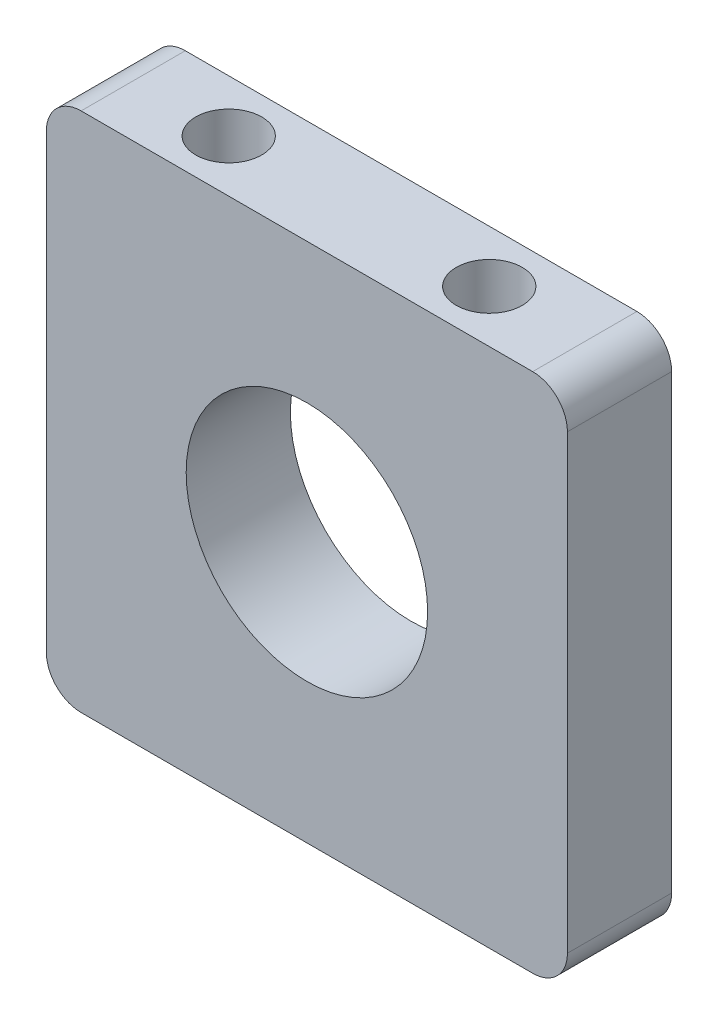
SolidWorks part; units mm, degrees
ref_plane "Front Plane" through (0, 0, 0) normal (0, 0, 1) x (1, 0, 0)
ref_plane "Top Plane" through (0, 0, 0) normal (0, 1, 0) x (1, 0, 0)
ref_plane "Right Plane" through (0, 0, 0) normal (1, 0, 0) x (0, 0, -1)
sketch "Sketch1" plane through (0, 0, 0) normal (0, 0, 1) x (1, 0, 0)
  line L1 (19.05, -19.05) -> (-19.05, -19.05)
  line L2 (19.05, -19.05) -> (19.05, 19.05)
  line L3 (19.05, 19.05) -> (-19.05, 19.05)
  line L4 (-19.05, -19.05) -> (-19.05, 19.05)
  line L5 (19.05, -19.05) -> (-19.05, 19.05) construction
  line L6 (19.05, 19.05) -> (-19.05, -19.05) construction
  circle A0 centre (0, 0) radius 8.8265
  point P0 (0, 0)
  dimension "D2" = 17.653
  dimension "D1" = 38.1
extrude "Boss-Extrude1" add sketch "Sketch1" along normal blind 7.62
fillet "Fillet1" radius 2.54 4 edges at (19.05, -19.05, 3.81) (-19.05, -19.05, 3.81) (-19.05, 19.05, 3.81) (19.05, 19.05, 3.81)
sketch "Sketch2" plane through (0, -19.05, 0) normal (0, -1, 0) x (1, 0, 0)
  line L0 (-16.51, 7.62) -> (-19.05, 7.62) construction
  line L1 (-19.05, 7.62) -> (-19.05, 0) construction
  line L2 (-19.05, 0) -> (-16.51, 0) construction
  line L3 (19.05, 7.62) -> (16.51, 7.62) construction
  line L4 (16.51, 0) -> (19.05, 0) construction
  line L5 (19.05, 0) -> (19.05, 7.62) construction
  line L6 (-16.51, 0) -> (16.51, 0) construction
  line L7 (16.51, 7.62) -> (-16.51, 7.62) construction
  line L8 (-16.51, 7.62) -> (-19.05, 7.62)
  line L9 (-19.05, 7.62) -> (-19.05, 0)
  line L10 (-19.05, 0) -> (-16.51, 0)
  line L11 (19.05, 7.62) -> (16.51, 7.62)
  line L12 (16.51, 0) -> (19.05, 0)
  line L13 (19.05, 0) -> (19.05, 7.62)
  line L14 (-16.51, 0) -> (16.51, 0)
  line L15 (16.51, 7.62) -> (-16.51, 7.62)
  line L16 (0, 0) -> (0, 7.62) construction
  line L17 (-9.525, 3.81) -> (9.525, 3.81) construction
  circle A0 centre (9.525, 3.81) radius 2.413
  circle A1 centre (-9.525, 3.81) radius 2.413
  point P14 (0, 3.81)
  point P15 (11.33, 3.81)
  point P16 (0, 3.81)
  dimension "D1" = 4.826
  dimension "D2" = 9.525
  dimension "D4" = 3.81
  dimension "D5" = 3.81
extrude "Cut-Extrude1" cut sketch "Sketch2" against normal blind 7.62 contours A0 | A1
sketch "Sketch3" plane through (0, 19.05, 0) normal (0, 1, 0) x (1, 0, 0)
  line L0 (16.51, -7.62) -> (19.05, -7.62) construction
  line L1 (19.05, -7.62) -> (19.05, 0) construction
  line L2 (19.05, 0) -> (16.51, 0) construction
  line L3 (-19.05, -7.62) -> (-16.51, -7.62) construction
  line L4 (-16.51, 0) -> (-19.05, 0) construction
  line L5 (-19.05, 0) -> (-19.05, -7.62) construction
  line L6 (16.51, 0) -> (-16.51, 0) construction
  line L7 (-16.51, -7.62) -> (16.51, -7.62) construction
  line L8 (16.51, -7.62) -> (19.05, -7.62)
  line L9 (19.05, -7.62) -> (19.05, 0)
  line L10 (19.05, 0) -> (16.51, 0)
  line L11 (-19.05, -7.62) -> (-16.51, -7.62)
  line L12 (-16.51, 0) -> (-19.05, 0)
  line L13 (-19.05, 0) -> (-19.05, -7.62)
  line L14 (16.51, 0) -> (-16.51, 0)
  line L15 (-16.51, -7.62) -> (16.51, -7.62)
  line L16 (0, 0) -> (0, -7.62) construction
  line L17 (0, -3.81) -> (9.525, -3.81) construction
  line L18 (0, -3.81) -> (-9.525, -3.81) construction
  circle A0 centre (-9.525, -3.81) radius 2.413
  circle A1 centre (9.525, -3.81) radius 2.413
  dimension "D5" = 4.826
  dimension "D1" = 9.525
  dimension "D2" = 3.81
  dimension "D4" = 3.81
extrude "Cut-Extrude2" cut sketch "Sketch3" against normal blind 7.62 contours A0 | A1
